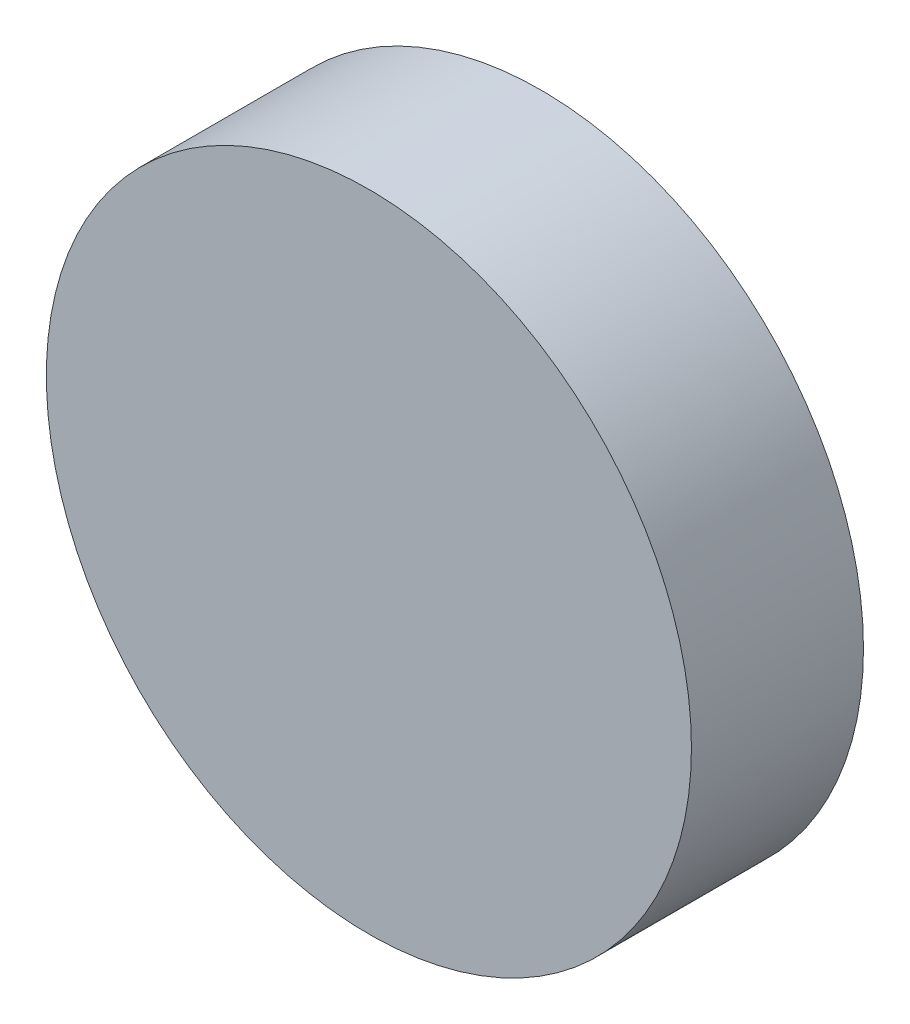
SolidWorks part; units mm, degrees
ref_plane "Front Plane" through (0, 0, 0) normal (0, 0, 1) x (1, 0, 0)
ref_plane "Top Plane" through (0, 0, 0) normal (0, 1, 0) x (1, 0, 0)
ref_plane "Right Plane" through (0, 0, 0) normal (1, 0, 0) x (0, 0, -1)
sketch "Sketch1" plane through (0, 0, 0) normal (0, 0, 1) x (1, 0, 0)
  circle A0 centre (0, 0) radius 4.5
  dimension "D1" = 9
extrude "Boss-Extrude1" add sketch "Sketch1" along normal blind 2.4
sketch "Sketch2" plane through (0, 0, 0) normal (0, 0, -1) x (-1, 0, 0)
  line L0 (-4.4981, -0.1323) -> (4.4977, 0.1452) construction
  circle A0 centre (0, 0) radius 4.5 construction
  circle A1 centre (2, 0.0682) radius 0.5
  circle A2 centre (-2, -0.0552) radius 0.5
  dimension "D1" = 1
  dimension "D2" = 1
  dimension "D3" = 2
  dimension "D4" = 2
extrude "Cut-Extrude1" cut sketch "Sketch2" against normal blind 0.5
